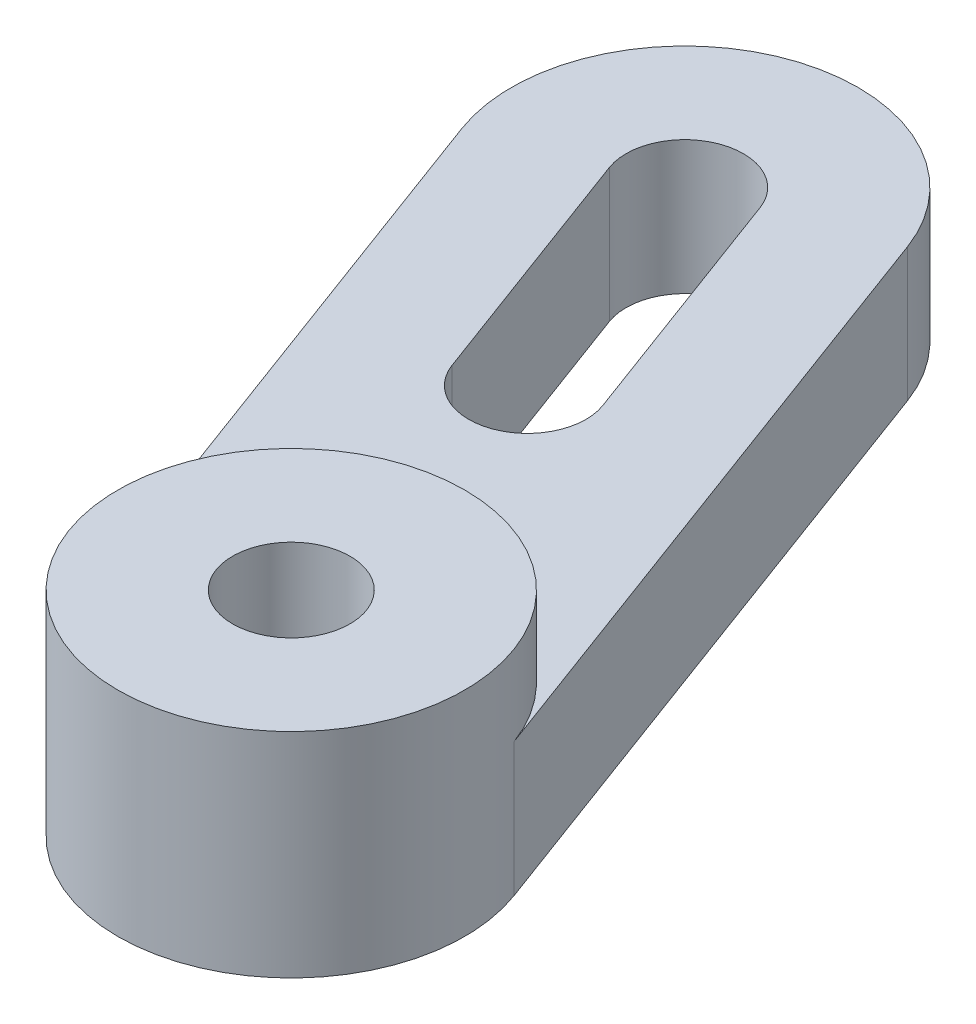
SolidWorks part; units mm, degrees
ref_plane "Front Plane" through (0, 0, 0) normal (0, 0, 1) x (1, 0, 0)
ref_plane "Top Plane" through (0, 0, 0) normal (0, 1, 0) x (1, 0, 0)
ref_plane "Right Plane" through (0, 0, 0) normal (1, 0, 0) x (0, 0, -1)
sketch "Sketch1" plane through (0, 0, 0) normal (0, 1, 0) x (1, 0, 0)
  line L0 (-7.0637, 0.4097) -> (-15.7556, 23.8501) construction
  line L1 (-13.1582, -1.8501) -> (-21.8501, 21.5902)
  line L2 (-0.9692, 2.6696) -> (-9.6611, 26.11)
  line L3 (-15.7556, 23.8501) -> (-12.2789, 14.474) construction
  line L4 (-13.6929, 24.615) -> (-10.2161, 15.2389)
  line L5 (-17.8184, 23.0852) -> (-14.3416, 13.7091)
  arc A0 (-13.1582, -1.8501) -> (-0.9692, 2.6696) centre (-7.0637, 0.4097) ccw
  arc A1 (-9.6611, 26.11) -> (-21.8501, 21.5902) centre (-15.7556, 23.8501) ccw
  arc A2 (-13.6929, 24.615) -> (-17.8184, 23.0852) centre (-15.7556, 23.8501) ccw
  arc A3 (-14.3416, 13.7091) -> (-10.2161, 15.2389) centre (-12.2789, 14.474) ccw
  circle A4 centre (-7.0637, 0.4097) radius 2.2
  point P1 (-11.4097, 12.1299)
  point P10 (-14.0172, 19.162)
  dimension "D1" = 4.4
extrude "Boss-Extrude1" add sketch "Sketch1" along normal blind 5
sketch "Sketch2" plane through (0, 5, 0) normal (0, 1, 0) x (-1, 0, 0)
  circle A0 centre (7.0637, -0.4097) radius 6.5
  circle A1 centre (7.0637, -0.4097) radius 2.2
extrude "Boss-Extrude2" add sketch "Sketch2" along normal blind 3
